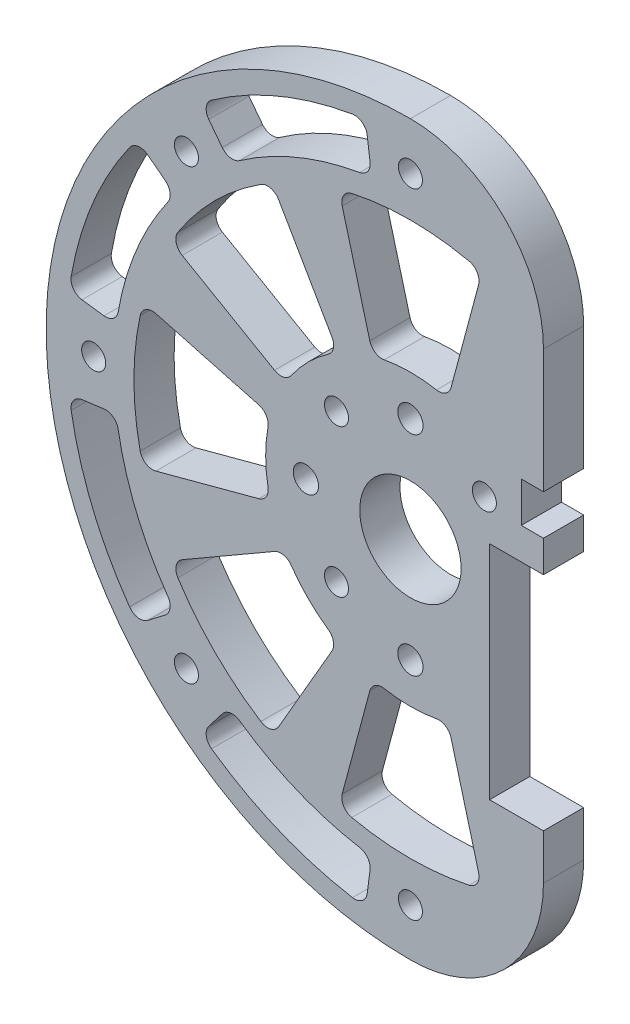
SolidWorks part; units mm, degrees
material "Balsa"
ref_plane "Front Plane" through (0, 0, 0) normal (0, 0, 1) x (1, 0, 0)
ref_plane "Top Plane" through (0, 0, 0) normal (0, 1, 0) x (1, 0, 0)
ref_plane "Right Plane" through (0, 0, 0) normal (1, 0, 0) x (0, 0, -1)
sketch "Sketch1" plane through (0, 0, 0) normal (0, 0, 1) x (1, 0, 0)
  line L0 (45.3154, 21.1309) -> (0, 0) construction
  line L1 (0, 0) -> (35.3553, -35.3553) construction
  line L2 (49.9788, 1.4542) -> (0, 0) construction
  line L3 (0, 0) -> (46.4674, -18.4603) construction
  circle A0 centre (45.3154, 21.1309) radius 1.8986
  circle A1 centre (49.9788, 1.4542) radius 1.9939
  circle A2 centre (0, 0) radius 57.5
  circle A3 centre (0, 0) radius 8
  circle A4 centre (0, 0) radius 16.5 construction
  circle A5 centre (46.4674, -18.4603) radius 1.9939
  circle A6 centre (0, 0) radius 50 construction
  circle A27 centre (0, -16.5) radius 1.9939
  circle A28 centre (11.6673, -11.6673) radius 1.8986 construction
  circle A30 centre (0, -50) radius 1.8986
  circle A31 centre (-16.5, 0) radius 1.9939
  circle A32 centre (-11.6673, -11.6673) radius 1.8986
  circle A33 centre (0, 16.5) radius 1.9939
  circle A34 centre (-11.6673, 11.6673) radius 1.8986
  circle A35 centre (16.5, 0) radius 1.9939 construction
  circle A36 centre (11.6673, 11.6673) radius 1.8986
  circle A38 centre (-35.3553, -35.3553) radius 1.8986
  circle A40 centre (-50, 0) radius 1.8986
  circle A42 centre (-35.3553, 35.3553) radius 1.8986
  circle A44 centre (0, 50) radius 1.8986
  circle A46 centre (35.3553, 35.3553) radius 1.8986 construction
  circle A48 centre (50, 0) radius 1.8986 construction
  circle A50 centre (35.3553, -35.3553) radius 1.8986
  dimension "D1" = 115
  dimension "D4" = 70
  dimension "D6" = 100
  dimension "D7" = 23.333
  dimension "D8" = 33
  dimension "D9" = 3.7973
  dimension "D10" = 3.9878
  dimension "D15" = 3.7973
  dimension "D17" = 3.9878
  dimension "D18" = 3.7973
  dimension "D3" = 16
  dimension "D11" = 3.9878
  dimension "D5" = 23.333
  dimension "D19" = 45
  dimension "D20" = 4
  dimension "D21" = 8
extrude "Boss-Extrude1" add sketch "Sketch1" along normal blind 6.35
sketch "Sketch2" plane through (0, 0, 0) normal (0, 0, 1) x (1, 0, 0)
  line L0 (12.5, -29.35) -> (41, -29.35)
  line L1 (41, -29.35) -> (41, 10.65)
  line L2 (41, 10.65) -> (44.5, 10.65)
  line L3 (44.5, 10.65) -> (44.5, 17)
  line L4 (44.5, 17) -> (41, 17)
  line L5 (41, 17) -> (41, 32)
  line L6 (41, 32) -> (21, 32)
  line L7 (21, 32) -> (21, 17)
  line L8 (21, 17) -> (17.5, 17)
  line L9 (17.5, 17) -> (17.5, 10.65)
  line L10 (17.5, 10.65) -> (21, 10.65)
  line L11 (21, 10.65) -> (21, 5.65)
  line L12 (21, 5.65) -> (12.5, 5.65)
  line L13 (12.5, 5.65) -> (12.5, -29.35)
  dimension "D1" = 20
  dimension "D2" = 3.5
  dimension "D3" = 3.5
  dimension "D4" = 15
  dimension "D5" = 6.35
  dimension "D6" = 5
  dimension "D7" = 40
  dimension "D8" = 8.5
  dimension "D9" = 32
  dimension "D10" = 21
extrude "Cut-Extrude1" cut sketch "Sketch2" along normal through all
sketch "Sketch3" plane through (0, 0, 0) normal (0, 0, -1) x (-1, 0, 0)
  line L0 (-41, 32) -> (-21, 32) construction
  line L1 (-34.175, -8) -> (-27.825, -8)
  line L2 (-34.175, -8) -> (-34.175, 72)
  line L3 (-34.175, 72) -> (-27.825, 72)
  line L4 (-27.825, -8) -> (-27.825, 72)
  line L5 (-34.175, -8) -> (-27.825, 72) construction
  line L6 (-34.175, 72) -> (-27.825, -8) construction
  point P0 (-31, 32)
  dimension "D1" = 6.35
  dimension "D2" = 80
extrude "Cut-Extrude3" cut sketch "Sketch3" against normal through all
sketch "Sketch4" plane through (0, 0, 0) normal (0, 0, 1) x (1, 0, 0)
  line L0 (21, -36.5) -> (21, -5.3721)
  line L1 (21, -5.3721) -> (24.175, -5.4115)
  line L2 (24.175, -5.4115) -> (24.175, -57.5)
  line L3 (0, -57.5) -> (24.175, -57.5)
  line L4 (0, 0) -> (82.9328, 0) construction
  line L5 (34.175, 32) -> (27.825, 32) construction
  line L6 (0, 57.5) -> (24.175, 57.5)
  line L7 (24.175, 5.4115) -> (24.175, 57.5)
  line L8 (21, 5.3721) -> (24.175, 5.4115)
  line L9 (21, 36.5) -> (21, 5.3721)
  arc A0 (0, -57.5) -> (21, -36.5) centre (0, -36.5) ccw
  arc A1 (0, 57.5) -> (21, 36.5) centre (0, 36.5) cw
  arc A2 (27.825, 50.3192) -> (34.175, 46.242) centre (0, 0) ccw construction
  point P13 (31, 32)
  point P16 (22.5875, -5.3918)
  dimension "D2" = 3.175
  dimension "D4" = 8.4125
extrude "Cut-Extrude5" cut sketch "Sketch4" along normal through all
sketch "Sketch6" plane through (0, 0, 6.35) normal (0, 0, 1) x (1, 0, 0)
  line L0 (0, 0) -> (-85.7599, 0) construction
  line L1 (-42.1627, -11.2975) -> (-22.0714, -5.914)
  line L2 (-42.1627, 11.2975) -> (-22.0714, 5.914)
  arc A0 (-22.0714, -5.914) -> (-22.0714, 5.914) centre (0, 0) cw
  arc A1 (-42.1627, -11.2975) -> (-42.1627, 11.2975) centre (0, 0) cw
  circle A2 centre (-16.5, 0) radius 1.9939 construction
  circle A3 centre (-50, 0) radius 1.8987 construction
  point P7 (-22.85, 0)
  point P8 (-43.65, 0)
  dimension "D1" = 6.35
  dimension "D2" = 6.35
  dimension "D3" = 30
extrude "Cut-Extrude7" cut sketch "Sketch6" against normal through all
fillet "Fillet1" radius 2 4 edges at (-42.1627, -11.2975, 3.175) (-22.0714, -5.914, 3.175) (-22.0714, 5.914, 3.175) (-42.1627, 11.2975, 3.175)
pattern_circular "CirPattern1" count 8 over 360 about axis through (0, 0, 0) along (0, 0, 1) skipping 3, 4, 5 of "Fillet1", "Cut-Extrude7"
sketch "Sketch7" plane through (0, 0, 6.35) normal (0, 0, 1) x (1, 0, 0)
  line L0 (0, 0) -> (-92.6914, 0) construction
  line L1 (0, 0) -> (-89.5535, 37.0943) construction
  line L2 (-43.0989, 33.071) -> (-37.1488, 28.5053)
  line L4 (-53.8602, 7.0908) -> (-46.4244, 6.1119)
  arc A0 (-53.8602, 7.0908) -> (-43.0989, 33.071) centre (0, 0) cw
  arc A1 (-46.4244, 6.1119) -> (-37.1488, 28.5053) centre (0, 0) cw
  circle A2 centre (-50, 0) radius 1.8987 construction
  circle A3 centre (-50, 0) radius 1.8986 construction
  arc A4 (-42.6565, 9.2598) -> (-42.6565, -9.2598) centre (0, 0) ccw construction
  arc A5 (0, 57.5) -> (0, -57.5) centre (0, 0) ccw construction
  point P11 (-43.2607, 17.9192)
  dimension "D3" = 3.175
  dimension "D4" = 3.175
  dimension "D1" = 22.5
  dimension "D2" = 30
extrude "Cut-Extrude8" cut sketch "Sketch7" against normal through all
fillet "Fillet2" radius 2 4 edges at (-53.8602, 7.0908, 3.175) (-46.4244, 6.1119, 3.175) (-37.1488, 28.5053, 3.175) (-43.0989, 33.071, 3.175)
pattern_circular "CirPattern2" count 8 over 360 about axis through (0, 0, 0) along (0, 0, 1) skipping 2, 3, 4, 5 of "Cut-Extrude8", "Fillet2"
